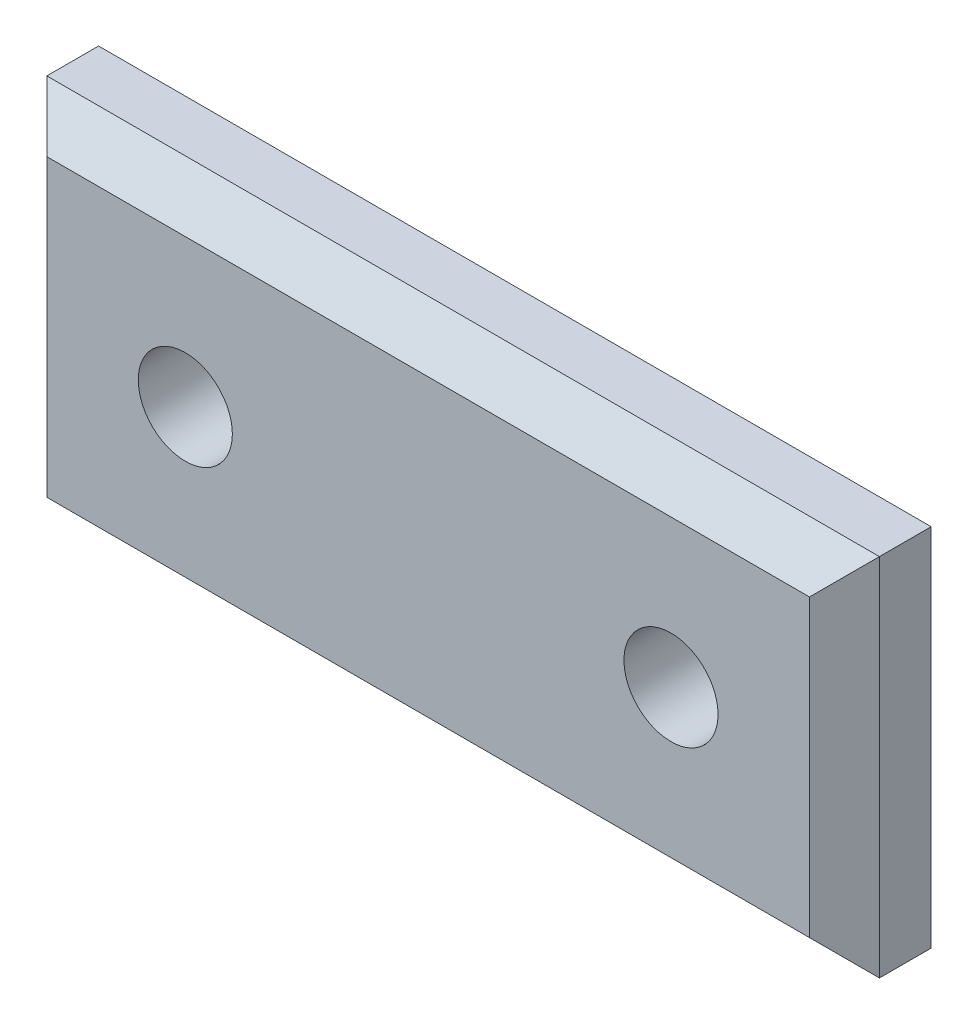
SolidWorks part; units mm, degrees
material "Copper"
ref_plane "Front Plane" through (0, 0, 0) normal (0, 0, 1) x (1, 0, 0)
ref_plane "Top Plane" through (0, 0, 0) normal (0, 1, 0) x (1, 0, 0)
ref_plane "Right Plane" through (0, 0, 0) normal (1, 0, 0) x (0, 0, -1)
sketch "Sketch2" plane through (0, 0, 0) normal (0, 0, 1) x (1, 0, 0)
  line L1 (-19.05, -8.3503) -> (19.05, -8.3503)
  line L2 (-19.05, -8.3503) -> (-19.05, 8.3502)
  line L3 (-19.05, 8.3502) -> (19.05, 8.3502)
  line L4 (19.05, -8.3503) -> (19.05, 8.3502)
  line L5 (-19.05, -8.3503) -> (19.05, 8.3502) construction
  line L6 (-19.05, 8.3502) -> (19.05, -8.3503) construction
  point P0 (0, 0)
  dimension "D1" = 38.1
  dimension "D2" = 16.7005
extrude "Boss-Extrude1" add sketch "Sketch2" along normal blind 3.9688
hole_wizard "#8 Clearance Hole1" positions "Sketch3" profile "Sketch4" hole size "#8" standard "ANSI Inch" end condition through all
sketch "Sketch3" plane through (0, 0, 3.9688) normal (0, 0, 1) x (1, 0, 0)
  line L0 (0, 8.3503) -> (0, -8.3503) construction
  line L1 (19.05, 8.3502) -> (-19.05, 8.3502) construction
  line L2 (-19.05, -8.3503) -> (19.05, -8.3503) construction
  line L3 (-19.05, 0) -> (19.05, 0) construction
  line L4 (-19.05, 8.3502) -> (-19.05, -8.3503) construction
  line L5 (19.05, -8.3503) -> (19.05, 8.3502) construction
  point P0 (-11.1125, 0)
  point P2 (11.1125, 0)
  dimension "D1" = 11.1125
  dimension "D2" = 11.1125
sketch "Sketch4" plane through (-11.1125, 0, 3.9688) normal (1, 0, 0) x (0, -1, 0)
  line L0 (0, 0) -> (0, 3.9688)
  line L1 (0, 3.9688) -> (2.1526, 3.9688)
  line L2 (2.1526, 3.9688) -> (2.1526, 0)
  line L5 (2.1526, 0) -> (0, 0)
  line L11 (0, -6.35) -> (0, 107.95) construction
  dimension "Thru Hole Dia." = 4.3053
  dimension "Thru Hole Depth" = 3.9688
chamfer "Chamfer1" distance 1.6002 angle 45 4 edges at (0, -8.3503, 3.9688) (19.05, 0, 3.9688) (0, 8.3502, 3.9688) (-19.05, 0, 3.9688)
